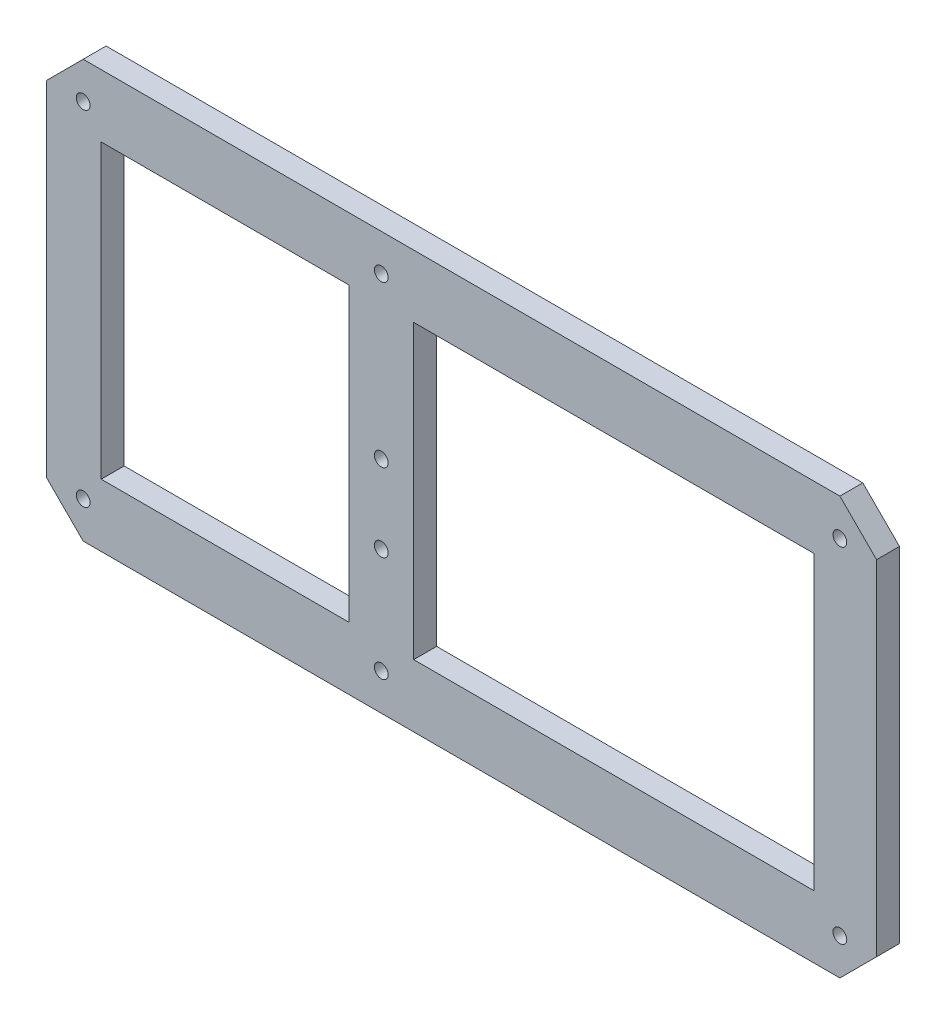
SolidWorks part; units mm, degrees
ref_plane "前视基准面" through (0, 0, 0) normal (0, 0, 1) x (1, 0, 0)
ref_plane "上视基准面" through (0, 0, 0) normal (0, 1, 0) x (1, 0, 0)
ref_plane "右视基准面" through (0, 0, 0) normal (1, 0, 0) x (0, 0, -1)
sketch "草图1" plane through (0, 0, 0) normal (0, 0, 1) x (1, 0, 0)
  line L0 (3.3152, -28.3102) -> (90.5873, -28.3102)
  line L10 (-3.7558, 49.033) -> (96.2442, 49.033)
  line L11 (104.2442, 41.033) -> (104.2442, -33.967)
  line L12 (-3.7558, 49.033) -> (-68.7558, 49.033)
  line L13 (-76.7558, 41.033) -> (-76.7558, -33.967)
  line L14 (-68.7558, -41.967) -> (96.2442, -41.967)
  line L22 (-64.8269, 35.3761) -> (-10.8269, 35.3761)
  line L26 (-64.8269, 35.3761) -> (-64.8269, -28.3102)
  line L27 (90.5873, -28.3102) -> (90.5873, 35.3761)
  line L28 (3.3152, 35.3761) -> (90.5873, 35.3761)
  line L29 (-64.8269, -28.3102) -> (-10.8269, -28.3102)
  line L31 (-10.8269, 28.3051) -> (-10.8269, -28.3102)
  line L32 (-10.8269, -28.3102) -> (-10.8269, 35.3761)
  line L33 (3.3152, 28.3051) -> (3.3152, -28.3102)
  line L34 (3.3152, -28.3102) -> (3.3152, 35.3761)
  line L35 (-68.7558, 49.033) -> (-76.7558, 41.033)
  line L38 (96.2442, 49.033) -> (104.2442, 41.033)
  line L41 (-76.7558, -33.967) -> (-68.7558, -41.967)
  line L44 (96.2442, -41.967) -> (104.2442, -33.967)
  circle A0 centre (-3.7558, 6.033) radius 1.5
  circle A1 centre (-3.7558, -10.967) radius 1.5
  circle A2 centre (-68.7558, 41.033) radius 1.5
  circle A3 centre (-3.7558, 41.033) radius 1.5
  circle A4 centre (-3.7558, -33.967) radius 1.5
  circle A5 centre (-68.7558, -33.967) radius 1.5
  circle A6 centre (96.2442, -33.967) radius 1.5
  circle A7 centre (96.2442, 41.033) radius 1.5
extrude "凸台-拉伸1" add sketch "草图1" along normal blind 5 contours L14 L44 L11 L38 L10 L12 L35 L13 L41 A7 A6 A5 A4 A3 A2 A1 A0 L33 L34 L28 L27 L0 L32 L31 L29 L26 L22
